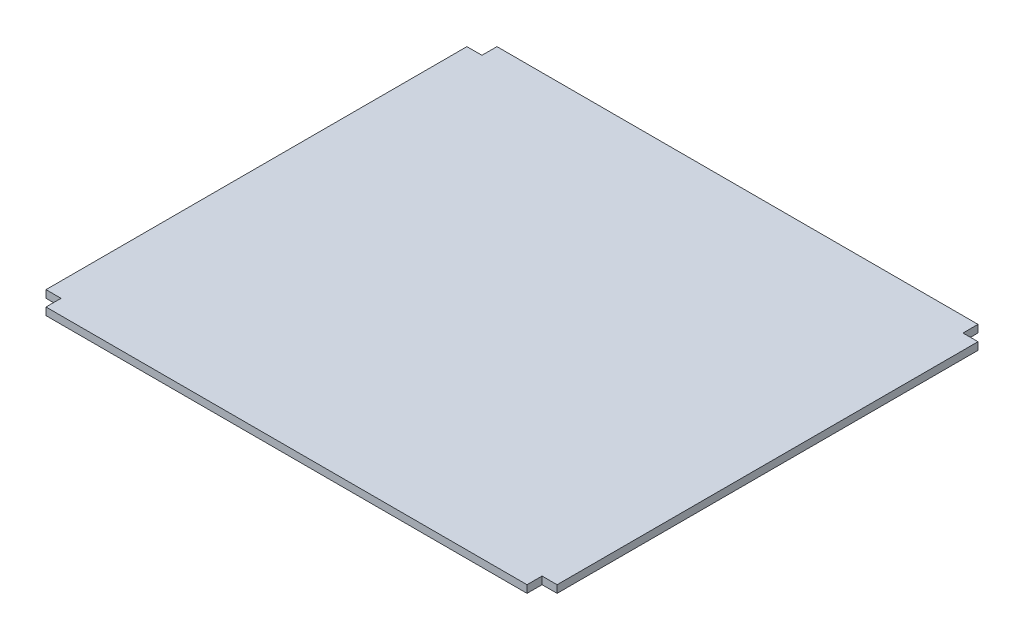
SolidWorks part; units mm, degrees
ref_plane "Front Plane" through (0, 0, 0) normal (0, 0, 1) x (1, 0, 0)
ref_plane "Top Plane" through (0, 0, 0) normal (0, 1, 0) x (1, 0, 0)
ref_plane "Right Plane" through (0, 0, 0) normal (1, 0, 0) x (0, 0, -1)
sketch "Sketch1" plane through (0, 0, 0) normal (0, 1, 0) x (1, 0, 0)
  line L0 (-320, 300) -> (-320, -300) construction
  line L1 (-340, 300) -> (340, 300)
  line L2 (-340, 300) -> (-340, -300)
  line L3 (-340, -300) -> (340, -300)
  line L4 (340, 300) -> (340, -300)
  line L5 (-340, 300) -> (340, -300) construction
  line L6 (-340, -300) -> (340, 300) construction
  line L7 (320, 300) -> (320, -300) construction
  line L8 (340, 280) -> (-340, 280) construction
  line L9 (340, -280) -> (-340, -280) construction
  line L10 (320, 300) -> (320, 280)
  line L11 (320, 280) -> (340, 280)
  line L12 (320, -300) -> (320, -280)
  line L13 (320, -280) -> (340, -280)
  line L14 (-320, -300) -> (-320, -280)
  line L15 (-320, -280) -> (-340, -280)
  line L16 (-340, 280) -> (-320, 280)
  line L17 (-320, 280) -> (-320, 300)
  point P0 (0, 0)
  dimension "D1" = 20
  dimension "D2" = 20
  dimension "D3" = 20
  dimension "D4" = 20
extrude "Boss-Extrude2" add sketch "Sketch1" along normal blind 10 contours L17 L16 L2 L15 L14 L3 L12 L13 L4 L11 L10 L1
